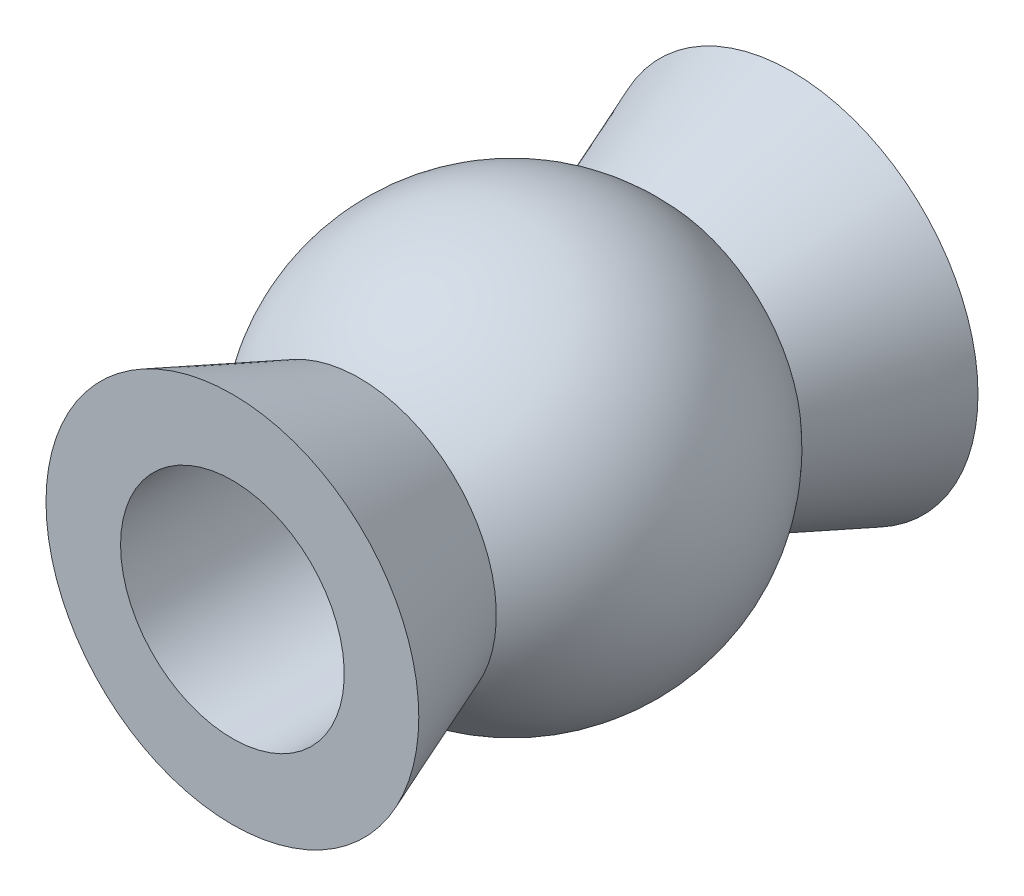
SolidWorks part; units mm, degrees
ref_plane "Alzado" through (0, 0, 0) normal (0, 0, 1) x (1, 0, 0)
ref_plane "Planta" through (0, 0, 0) normal (0, 1, 0) x (1, 0, 0)
ref_plane "Vista lateral" through (0, 0, 0) normal (1, 0, 0) x (0, 0, -1)
sketch "Croquis3" plane through (0, 0, 0) normal (0, 1, 0) x (1, 0, 0)
  line L1 (0, 3.75) -> (2.5, 3.75)
  line L4 (0, 3.75) -> (0, -3.75) construction
  line L5 (2.5, 3.75) -> (2, 2.4664)
  line L6 (0, -3.75) -> (0, 3.75)
  line L7 (2, 2.4664) -> (1.8366, 2.0468)
  line L8 (0, -3.75) -> (2.5, -3.75)
  line L9 (2, -2.4664) -> (1.8366, -2.0468)
  line L10 (2.5, -3.75) -> (2, -2.4664)
  arc A0 (1.8366, -2.0468) -> (1.8366, 2.0468) centre (0, 0) ccw
  dimension "D1" = 5.5
  dimension "D3" = 2.5
revolve "Revolución3" add sketch "Croquis3" angle 360 about L4
sketch "Croquis5" plane through (0, 0, -3.75) normal (0, 0, -1) x (-1, 0, 0)
  circle A0 centre (0, 0) radius 1.5
  dimension "D1" = 3
extrude "Cortar-Extruir3" cut sketch "Croquis5" against normal blind 10
